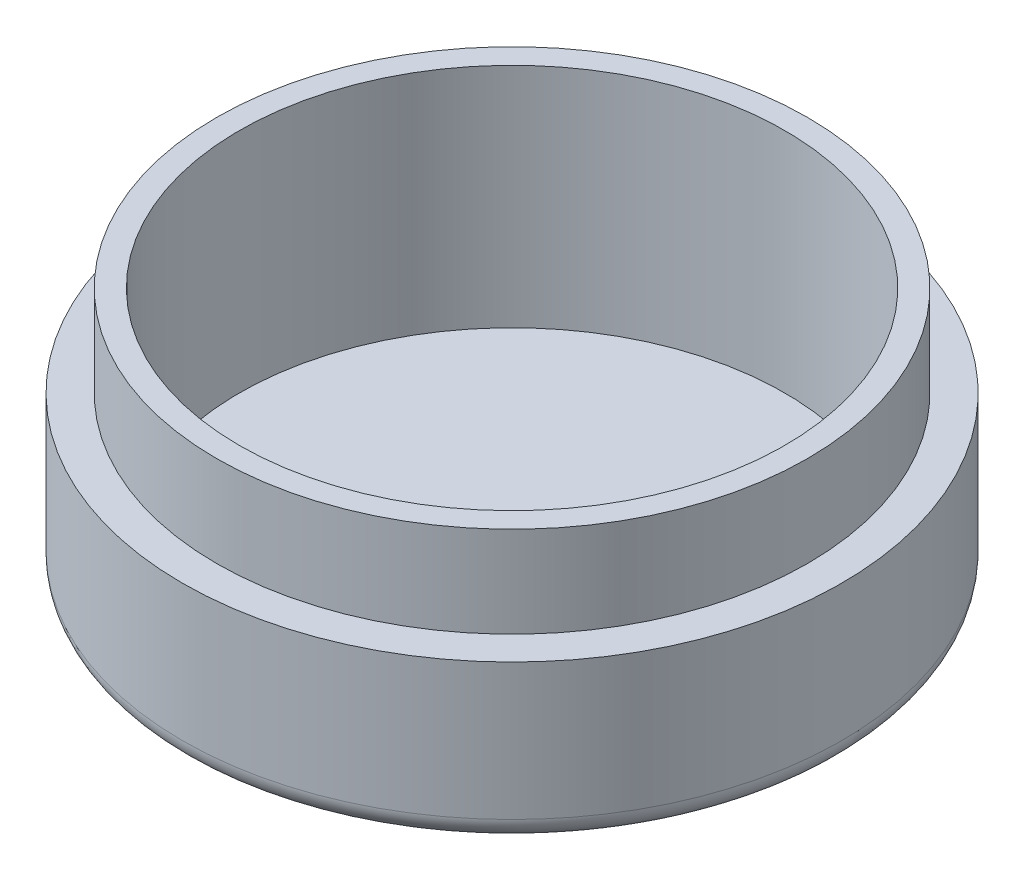
SolidWorks part; units mm, degrees
ref_plane "Front Plane" through (0, 0, 0) normal (0, 0, 1) x (1, 0, 0)
ref_plane "Top Plane" through (0, 0, 0) normal (0, 1, 0) x (1, 0, 0)
ref_plane "Right Plane" through (0, 0, 0) normal (1, 0, 0) x (0, 0, -1)
sketch "Sketch1" plane through (0, 0, 0) normal (0, 1, 0) x (1, 0, 0)
  circle A0 centre (0, 0) radius 14.5
  dimension "D1" = 29
extrude "Boss-Extrude1" add sketch "Sketch1" along normal blind 1
sketch "Sketch2" plane through (0, 1, 0) normal (0, 1, 0) x (1, 0, 0)
  circle A0 centre (0, 0) radius 14.5
  circle A1 centre (0, 0) radius 12
  dimension "D1" = 29
  dimension "D2" = 24
extrude "Boss-Extrude2" add sketch "Sketch2" along normal blind 6
sketch "Sketch3" plane through (0, 7, 0) normal (0, 1, 0) x (1, 0, 0)
  circle A0 centre (0, 0) radius 12
  circle A1 centre (0, 0) radius 13
  dimension "D1" = 24
  dimension "D2" = 26
extrude "Boss-Extrude3" add sketch "Sketch3" along normal blind 4
fillet "Fillet1" radius 1 1 edges at (0, 0, 14.5)
